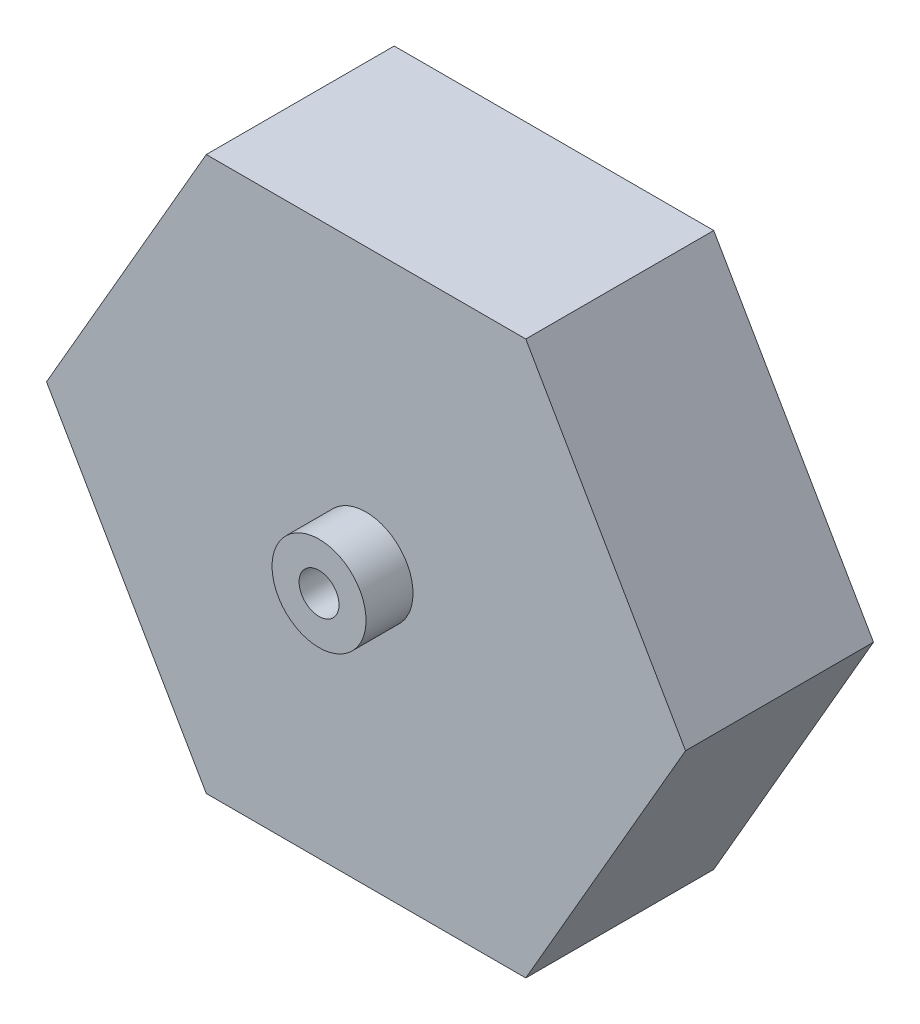
SolidWorks part; units mm, degrees
ref_plane "Front Plane" through (0, 0, 0) normal (0, 0, 1) x (1, 0, 0)
ref_plane "Top Plane" through (0, 0, 0) normal (0, 1, 0) x (1, 0, 0)
ref_plane "Right Plane" through (0, 0, 0) normal (1, 0, 0) x (0, 0, -1)
sketch "Sketch1" plane through (0, 0, 0) normal (0, 0, 1) x (1, 0, 0)
  line L0 (0, 16.3868) -> (0, -14.5333) construction
  line L1 (3.4, 0) -> (-3.4, 0)
  line L2 (-3.4, 0) -> (-6.8, -5.889)
  line L3 (-6.8, -5.889) -> (-3.4, -11.7779)
  line L4 (-3.4, -11.7779) -> (3.4, -11.7779)
  line L5 (6.8, -5.889) -> (3.4, -11.7779)
  line L6 (3.4, 0) -> (6.8, -5.889)
  point P9 (0, -11.7779)
  point P11 (0, 0)
  dimension "D1" = 3.4
  dimension "D2" = 6.8
  dimension "D3" = 6.8
  dimension "D4" = 3.4
  dimension "D5" = 120
  dimension "D6" = 120
  dimension "D7" = 120
extrude "Boss-Extrude1" add sketch "Sketch1" along normal blind 4
sketch "Sketch2" plane through (0, 0, 4) normal (0, 0, 1) x (1, 0, 0)
  line L0 (-6.8, -5.889) -> (6.8, -5.889) construction
  line L1 (0, 0) -> (0, -5.889) construction
  line L2 (0, -5.889) -> (0, -11.7779) construction
  line L3 (-3.4, -11.7779) -> (3.4, -11.7779) construction
  circle A0 centre (0, -5.889) radius 1
  circle A1 centre (0, -5.889) radius 0.425
  dimension "D1" = 2
  dimension "D2" = 0.85
extrude "Boss-Extrude2" add sketch "Sketch2" along normal blind 1
sketch "Sketch6" plane through (0, 0, 4) normal (0, 0, 1) x (1, 0, 0)
  circle A0 centre (0, -5.889) radius 0.425
extrude "Cut-Extrude1" cut sketch "Sketch6" against normal blind 63
